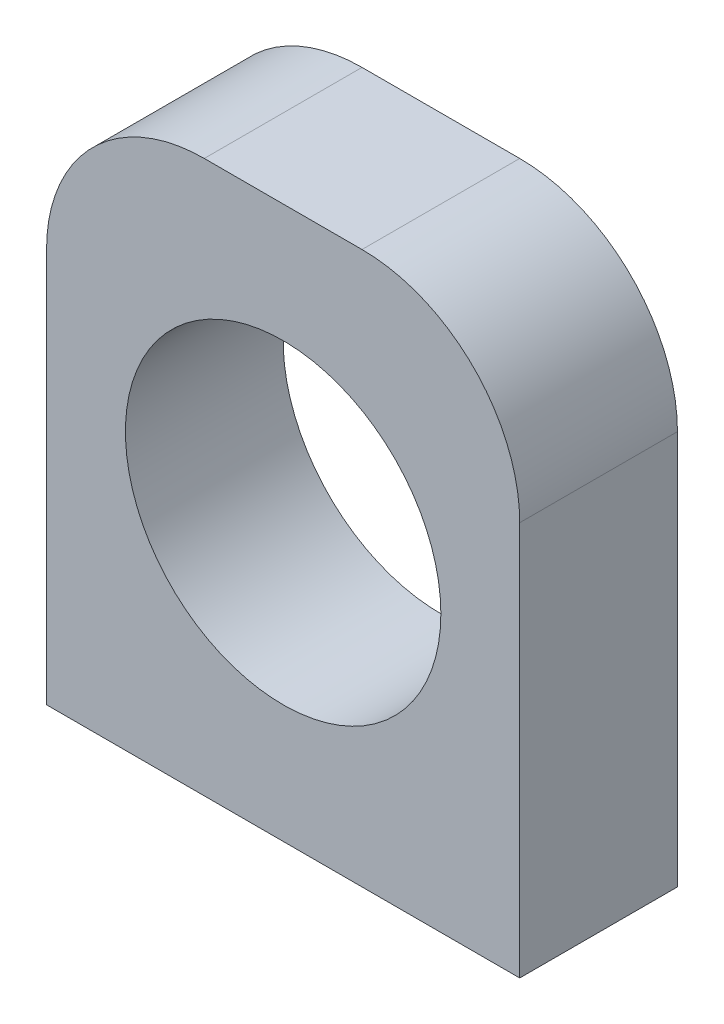
SolidWorks part; units mm, degrees
material "6061-T6 (SS)"
ref_plane "Front Plane" through (0, 0, 0) normal (0, 0, 1) x (1, 0, 0)
ref_plane "Top Plane" through (0, 0, 0) normal (0, 1, 0) x (1, 0, 0)
ref_plane "Right Plane" through (0, 0, 0) normal (1, 0, 0) x (0, 0, -1)
sketch "Sketch1" plane through (0, 0, 0) normal (0, 0, 1) x (1, 0, 0)
  line L1 (38.1, -44.45) -> (-38.1, -44.45)
  line L2 (38.1, -44.45) -> (38.1, 19.05)
  line L3 (12.7, 44.45) -> (-12.7, 44.45)
  line L4 (-38.1, -44.45) -> (-38.1, 19.05)
  line L5 (38.1, -44.45) -> (-38.1, 44.45) construction
  line L6 (38.1, 44.45) -> (-38.1, -44.45) construction
  arc A0 (38.1, 19.05) -> (12.7, 44.45) centre (12.7, 19.05) ccw
  arc A1 (-12.7, 44.45) -> (-38.1, 19.05) centre (-12.7, 19.05) ccw
  circle A2 centre (0, 0) radius 25.4
  point P0 (0, 0)
  dimension "D1" = 25.4
  dimension "D4" = 50.8
  dimension "D2" = 76.2
  dimension "D3" = 88.9
extrude "Boss-Extrude1" add sketch "Sketch1" along normal mid plane 25.4
sketch "Sketch2" plane through (0, -44.45, 0) normal (0, -1, 0) x (1, 0, 0)
  line L1 (19.05, -7.9375) -> (-19.05, -7.9375) construction
  line L2 (19.05, -7.9375) -> (19.05, 7.9375) construction
  line L3 (19.05, 7.9375) -> (-19.05, 7.9375) construction
  line L4 (-19.05, -7.9375) -> (-19.05, 7.9375) construction
  line L5 (19.05, -7.9375) -> (-19.05, 7.9375) construction
  line L6 (19.05, 7.9375) -> (-19.05, -7.9375) construction
  point P0 (0, 0)
  point P7 (-19.05, 7.9375)
  point P8 (19.05, 7.9375)
  point P9 (19.05, -7.9375)
  point P10 (-19.05, -7.9375)
  dimension "D1" = 15.875
  dimension "D2" = 38.1
hole_wizard "#10-32 Tapped Hole1" positions "Sketch4" profile "Sketch3" tap size "#10-32" standard "ANSI Inch"
sketch "Sketch4" plane through (0, -44.45, 0) normal (0, -1, 0) x (-1, 0, 0)
  point P0 (19.05, -7.9375)
  point P3 (-19.05, -7.9375)
  point P6 (-19.05, 7.9375)
  point P9 (19.05, 7.9375)
sketch "Sketch3" plane through (-19.05, -44.45, 7.9375) normal (1, 0, 0) x (0, 0, -1)
  line L0 (0, 0) -> (0, 13.2428)
  line L1 (0, 13.2428) -> (2.0193, 12.0294)
  line L2 (2.0193, 12.0294) -> (2.0193, 0)
  line L5 (2.0193, 0) -> (0, 0)
  line L10 (0, 13.2428) -> (-2.0193, 12.0294) construction
  line L11 (0, -6.35) -> (0, 107.95) construction
  dimension "Tap Drill Dia." = 4.0386
  dimension "Tap Drill Depth" = 12.0294
  dimension "Drill Angle" = 118
cosmetic thread "Hole Thread1" parameters "D1"=9.652, "D2"=4.826
cosmetic thread "Hole Thread2" parameters "D1"=9.652, "D2"=4.826
cosmetic thread "Hole Thread3" parameters "D1"=9.652, "D2"=4.826
cosmetic thread "Hole Thread4" parameters "D1"=9.652, "D2"=4.826
